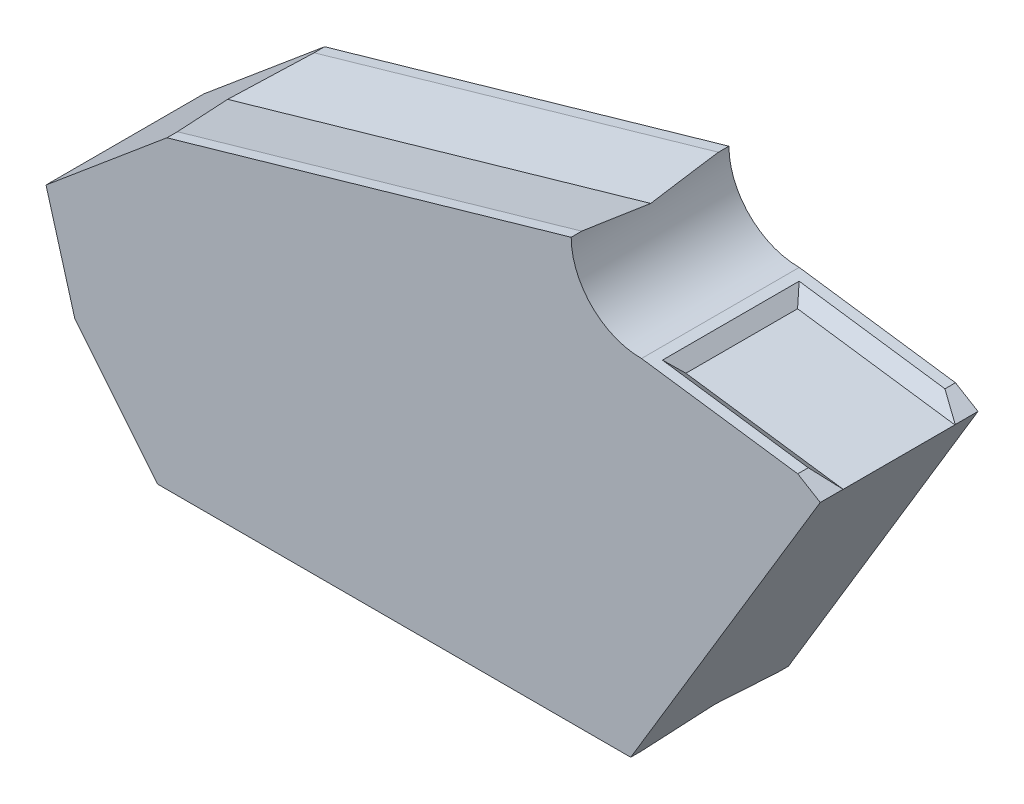
SolidWorks part; units mm, degrees
ref_plane "Front Plane" through (0, 0, 0) normal (0, 0, 1) x (1, 0, 0)
ref_plane "Top Plane" through (0, 0, 0) normal (0, 1, 0) x (1, 0, 0)
ref_plane "Right Plane" through (0, 0, 0) normal (1, 0, 0) x (0, 0, -1)
sketch "Sketch1" plane through (0, 0, 0) normal (0, 0, 1) x (1, 0, 0)
  line L0 (0, 0) -> (9, 0)
  line L1 (9, 0) -> (12.6056, 6)
  line L2 (12.6056, 6) -> (12.177, 6.2575)
  line L3 (12.177, 6.2575) -> (9.2057, 6.6714)
  line L5 (7.8683, 8) -> (0.1787, 5.7931)
  line L6 (0.1787, 5.7931) -> (-2.1206, 3.8662)
  line L7 (-2.1206, 3.8662) -> (-1.5739, 1.9424)
  line L8 (-1.5739, 1.9424) -> (0, 0)
  arc A0 (7.8683, 8) -> (9.2057, 6.6714) centre (9.1969, 8) ccw
  dimension "D1" = 0.5
  dimension "D2" = 3
  dimension "D3" = 8
  dimension "D4" = 3
  dimension "D5" = 2
  dimension "D6" = 2.5
  dimension "D7" = 7
  dimension "D8" = 9
  dimension "D9" = 6
extrude "Extrude1" add sketch "Sketch1" along normal blind 3
sketch "Sketch2" plane through (1.0868, 7.8023, 0) normal (0.138, 0.9904, 0) x (0.9904, -0.138, 0)
  line L1 (12.7557, -0.2) -> (8.3973, -0.2)
  line L3 (12.7557, -2.8) -> (8.3973, -2.8)
  line L4 (8.3973, -0.2) -> (8.3973, -2.8)
  line L5 (11.1973, 0) -> (8.1973, 0) construction
  line L6 (11.1973, -3) -> (8.1973, -3) construction
  line L7 (8.1973, -3) -> (8.1973, 0) construction
  line L8 (12.7557, -2.8) -> (12.7557, -0.2)
  dimension "D1" = 0.2
  dimension "D2" = 0.2
  dimension "D3" = 0.2
extrude "Extrude2" cut sketch "Sketch2" against normal blind 0.2 draft 50
sketch "Sketch3" plane through (-1.5225, 5.3049, 0) normal (-0.2759, 0.9612, 0) x (0.9612, 0.2759, 0)
  line L1 (-1.9667, -0.2) -> (14.6789, -0.2)
  line L3 (-1.9667, -2.8) -> (14.6789, -2.8)
  line L6 (9.7699, 0) -> (1.7699, 0) construction
  line L7 (9.7699, -3) -> (1.7699, -3) construction
  line L8 (14.6789, -0.2) -> (14.6789, -2.8)
  line L9 (-1.9667, -0.2) -> (-1.9667, -2.8)
  dimension "D1" = 0.2
  dimension "D2" = 0.2
extrude "Extrude3" cut sketch "Sketch3" against normal blind 0.2 draft 82
sketch "Sketch4" plane through (0, 0, 0) normal (0, -1, 0) x (1, 0, 0)
  line L0 (0, 0) -> (9, 0) construction
  line L1 (13.7314, 0.2) -> (-3.3872, 0.2)
  line L2 (13.7314, 0.2) -> (13.7314, 2.8)
  line L3 (13.7314, 2.8) -> (-3.3872, 2.8)
  line L4 (-3.3872, 0.2) -> (-3.3872, 2.8)
  line L5 (0, 3) -> (9, 3) construction
  dimension "D1" = 0.2
  dimension "D2" = 0.2
extrude "Extrude4" cut sketch "Sketch4" against normal blind 0.2 draft 82
